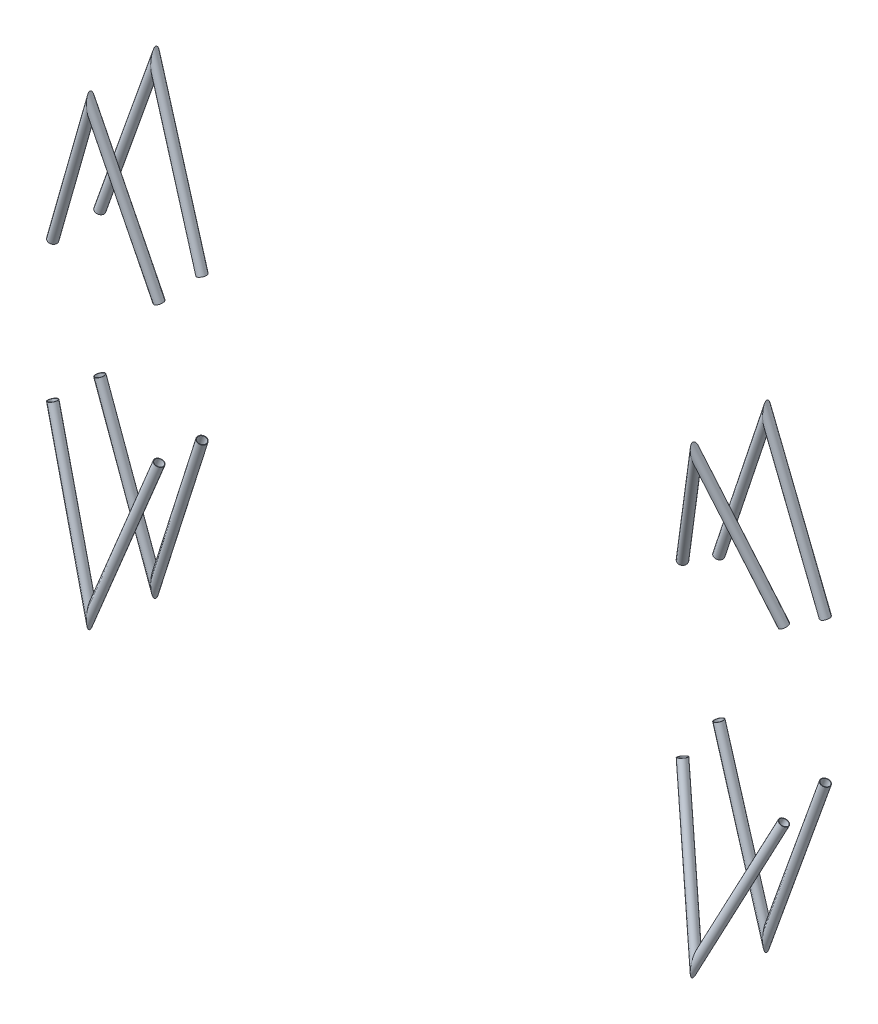
SolidWorks part; units mm, degrees
material "AISI 1015 Steel, Cold Drawn (SS)"
material "AISI 1015 Steel, Cold Drawn (SS)"
material "AISI 1015 Steel, Cold Drawn (SS)"
material "AISI 1015 Steel, Cold Drawn (SS)"
material "AISI 1015 Steel, Cold Drawn (SS)"
material "AISI 1015 Steel, Cold Drawn (SS)"
material "AISI 1015 Steel, Cold Drawn (SS)"
material "AISI 1015 Steel, Cold Drawn (SS)"
material "AISI 1015 Steel, Cold Drawn (SS)"
ref_plane "Ground Plane" through (0, 0, 0) normal (0, 0, 1) x (1, 0, 0)
ref_plane "Side Plane" through (0, 0, 0) normal (0, 1, 0) x (1, 0, 0)
ref_plane "Rear Axel Centerline" through (0, 0, 0) normal (1, 0, 0) x (0, 0, -1)
ref_plane "Front Axel Centerline" through (1700, 0, 0) normal (1, 0, 0) x (0, 0, -1)
sketch "Chassis Side View" plane through (0, 0, 0) normal (0, 1, 0) x (1, 0, 0)
  line L0 (0, -100.53) -> (1700, -100.53) construction
  line L1 (850, -100.53) -> (850, -280)
  line L2 (0, -127.1843) -> (0, 127.1843) construction
  line L3 (-786.3928, 0) -> (786.3928, 0) construction
  line L4 (1550, -100.53) -> (1550, -346.3589) construction
  line L5 (1550, -100.53) -> (1550, -595.53) construction
  line L6 (650, -100.53) -> (650, -1216.53) construction
  line L7 (150, -100.53) -> (150, -312.2598) construction
  line L8 (-150, -100.53) -> (-150, -312.2598) construction
  line L9 (1850, -100.53) -> (1850, -346.3589) construction
  line L10 (0, -100.53) -> (150, -100.53) construction
  line L11 (1700, -100.53) -> (2450, -100.53) construction
  line L12 (2450, -100.53) -> (2450, -450.53) construction
  line L13 (2450, -450.53) -> (1550, -545.53) construction
  line L14 (150, -100.53) -> (150, -400.53) construction
  dimension "D1" = 1700
  dimension "D3" = 850
  dimension "D4" = 100.53
  dimension "D5" = 150
  dimension "D6" = 150
  dimension "D7" = 150
  dimension "D8" = 150
  dimension "D2" = 280
  dimension "D9" = 900
  dimension "D10" = 1116
  dimension "D11" = 495
  dimension "D12" = 350
  dimension "D13" = 900
  dimension "D14" = 50
  dimension "D15" = 300
  dimension "D16" = 500
sketch "Front Wheel Assy Constraints" plane through (1700, 0, 0) normal (1, 0, 0) x (0, 0, -1)
  line L0 (1.6623, 571.529) -> (-1.6623, 762)
  line L2 (-1.6623, 762) -> (-222.6087, 758.1434)
  line L3 (-451.1739, 754.1537) -> (-447.8492, 563.6828)
  line L4 (-222.6087, 758.1434) -> (-451.1739, 754.1537)
  line L5 (-447.8492, 563.6828) -> (-333.5666, 565.6776)
  line L10 (-105.0014, 569.6672) -> (1.6623, 571.529)
  line L11 (-449.5115, 658.9183) -> (0, 666.7645) construction
  line L12 (-222.6087, 758.1434) -> (-221.0572, 669.2569) construction
  line L13 (-107.0128, 684.8996) -> (-335.578, 680.91)
  line L14 (-335.578, 680.91) -> (-333.5666, 565.6776)
  line L15 (-107.0128, 684.8996) -> (-105.0014, 569.6672)
  line L16 (0, 786.3928) -> (0, -786.3928) construction
  line L17 (0, 0) -> (-792.1695, 0) construction
  point P12 (-221.2954, 682.9048)
  dimension "D1" = 190.5
  dimension "D2" = 228.6
  dimension "D3" = 220.98
  dimension "D4" = 228.6
  dimension "D5" = 20
  dimension "D6" = 1
  dimension "D7" = 1524
sketch "Rear Wheel Assy Constaints" plane through (0, 0, 0) normal (1, 0, 0) x (0, 0, -1)
  line L0 (-447.8492, 563.6828) -> (-451.1739, 754.1537)
  line L1 (-451.1739, 754.1537) -> (-222.6087, 758.1434)
  line L2 (-1.6623, 762) -> (1.6623, 571.529)
  line L3 (1.6623, 571.529) -> (-105.0014, 569.6672)
  line L4 (-105.0014, 569.6672) -> (-107.0128, 684.8996)
  line L5 (-107.0128, 684.8996) -> (-335.578, 680.91)
  line L6 (-335.578, 680.91) -> (-333.5666, 565.6776)
  line L7 (-333.5666, 565.6776) -> (-447.8492, 563.6828)
  line L8 (-449.5115, 658.9183) -> (0, 666.7645) construction
  line L9 (0, 0) -> (-789.3704, 0) construction
  line L10 (-221.0572, 669.2569) -> (-222.6087, 758.1434) construction
  line L11 (0, 786.3928) -> (0, -786.3928) construction
  line L12 (-0.0435, 669.2569) -> (-772.6175, 669.2569) construction
  line L13 (-222.6087, 758.1434) -> (-1.6623, 762)
  point P18 (-106.0071, 627.2834)
  point P19 (-221.2954, 682.9048)
  dimension "D1" = 228.6
  dimension "D2" = 220.98
  dimension "D3" = 20
  dimension "D4" = 1524
  dimension "D5" = 1
  dimension "D6" = 228.6
  dimension "D7" = 190.5
sketch "Front Sus Front View" plane through (1700, 0, 0) normal (1, 0, 0) x (0, 0, -1)
  line L0 (0, 666.7645) -> (0, 641.3645) construction
  line L1 (0, 641.3645) -> (-437.8219, 641.3645) construction
  line L2 (0, 641.3645) -> (-427.6307, 603.9517) construction
  line L3 (-305.1173, 614.6702) -> (-210.3608, 238.5)
  line L4 (-73.9022, -303.2224) -> (0, 666.7645) construction
  line L5 (-73.9022, -303.2224) -> (-101.6418, 200.0264) construction
  line L6 (-210.3608, 238.5) -> (-73.9022, -303.2224) construction
  line L7 (-101.6418, 200.0264) -> (-125.3644, 630.3965)
  line L8 (0, 0) -> (-50.8, 0) construction
  line L12 (-222.6087, 758.1434) -> (-221.0572, 669.2569) construction
  dimension "D1" = 25.4
  dimension "D2" = 5
  dimension "D4" = 969.9869
  dimension "D5" = 95
  dimension "D6" = 85
  dimension "D7" = 477
  dimension "D8" = 387.9211
  dimension "D9" = 431.0235
  dimension "D3" = 50.8
sketch "Rear Sus Front View" plane through (0, 0, 0) normal (1, 0, 0) x (0, 0, -1)
  line L0 (0, 666.7645) -> (0, 641.3645) construction
  line L1 (0, 641.3645) -> (-652.2854, 641.3645) construction
  line L2 (0, 641.3645) -> (-647.6734, 584.7004) construction
  line L3 (-305.1173, 614.6702) -> (-263.5724, 194.7562)
  line L4 (-166.3015, -788.4055) -> (-137.7828, 200) construction
  line L5 (-166.3015, -788.4055) -> (0, 666.7645) construction
  line L6 (-263.5724, 194.7562) -> (-166.3015, -788.4055) construction
  line L7 (-137.7828, 200) -> (-125.3644, 630.3965)
  line L8 (0, 0) -> (-76.2, 0) construction
  line L9 (-221.0572, 669.2569) -> (-222.6087, 758.1434) construction
  dimension "D1" = 25.4
  dimension "D2" = 5
  dimension "D5" = 95
  dimension "D6" = 85
  dimension "D3" = 76.2
  dimension "D4" = 1455.17
  dimension "D7" = 400
  dimension "D8" = 430.5757
  dimension "D9" = 421.9641
ref_plane "Front Wheel Side View Plane" through (0, 669.2569, 0) normal (0, 1, 0) x (1, 0, 0)
sketch "Front SVSA" plane through (0, 669.2569, 0) normal (0, 1, 0) x (1, 0, 0)
  line L0 (1731.3585, 77.2994) -> (1668.6415, -519.4137)
  line L1 (1700, -0.0435) -> (-2300, -97.8014) construction
  line L2 (1700, -0.0435) -> (1700, -815.7612) construction
  line L3 (-2300, -97.8014) -> (1700, -221.0572) construction
  line L6 (-786.3928, 0) -> (786.3928, 0) construction
  point P5 (1700, -221.0572)
  dimension "D1" = 600
  dimension "D2" = 6
  dimension "D3" = 1.4
  dimension "D4" = 4000
ref_plane "Rear Wheel Side View Plane" through (0, 669.2569, 0) normal (0, 1, 0) x (1, 0, 0)
sketch "Rear SVSA" plane through (0, 669.2569, 0) normal (0, 1, 0) x (1, 0, 0)
  line L0 (0, -0.0435) -> (0, -772.6175) construction
  line L3 (0, -221.0572) -> (4820.2153, -353.1722) construction
  line L4 (4820.2153, -353.1722) -> (0, -0.0435) construction
  line L5 (-786.3928, 0) -> (786.3928, 0) construction
  line L6 (0, -127.1843) -> (0, 127.1843) construction
  dimension "D1" = 4.19
  dimension "D2" = 1.57
  dimension "D3" = 4820.2153
sketch3d "Front Chassis Side Axis"
  line L0 (1700, 200.0264, 101.6418) -> (1700, 630.3965, 125.3644) construction
  line L1 (1700, 614.6702, 305.1173) -> (1700, 238.5, 210.3608) construction
  line L2 (1700, 200.0264, 101.6418) -> (1700, 630.3965, 125.3644) construction
  line L3 (1700, 614.6702, 305.1173) -> (1700, 238.5, 210.3608) construction
  line L4 (1700, 614.6702, 305.1173) -> (1700, 669.2569, 318.8676) construction
  line L5 (1700, 630.3965, 125.3644) -> (1700, 669.2569, 127.5064) construction
  line L6 (-2300, 669.2569, 97.8014) -> (1749.9238, 669.2569, 321.6267) construction
  line L7 (-2300, 669.2569, 97.8014) -> (1749.9986, 669.2569, 127.8777) construction
  line L8 (1749.9238, 669.2569, 321.6267) -> (1355.9629, 238.5, 191.3471) construction
  line L9 (1749.9986, 669.2569, 127.8777) -> (1146.276, 200.0264, 97.5298) construction
  line L10 (1700, 238.5, 210.3608) -> (1700, 238.5, 191.3471) construction
  line L11 (1700, 238.5, 191.3471) -> (1355.9629, 238.5, 191.3471) construction
  line L12 (1999.5429, 238.5, 226.9155) -> (1056.42, 238.5, 174.7924)
  line L13 (1700, 200.0264, 101.6418) -> (1700, 200.0264, 97.5298) construction
  line L14 (1700, 200.0264, 97.5298) -> (582.2888, 200.0264, 97.5298) construction
  line L15 (1999.9917, 200.0264, 103.8697) -> (846.2843, 200.0264, 95.3019)
  dimension "D1" = 50
  dimension "D2" = 50
  dimension "D3" = 300
  dimension "D4" = 300
  dimension "D5" = 300
  dimension "D6" = 300
sketch3d "Rear Chassis Side Axis"
  line L0 (0, 200, 137.7828) -> (0, 630.3965, 125.3644) construction
  line L1 (0, 614.6702, 305.1173) -> (0, 194.7562, 263.5724) construction
  line L2 (0, 200, 137.7828) -> (0, 630.3965, 125.3644) construction
  line L3 (0, 614.6702, 305.1173) -> (0, 194.7562, 263.5724) construction
  line L4 (0, 614.6702, 305.1173) -> (0, 669.2569, 310.5179) construction
  line L5 (0, 630.3965, 125.3644) -> (0, 669.2569, 124.2431) construction
  line L6 (4820.2153, 669.2569, 353.1722) -> (-24.999, 669.2569, 310.2967) construction
  line L7 (4820.2153, 669.2569, 353.1722) -> (-19.9775, 669.2569, 123.2943) construction
  line L8 (-24.999, 669.2569, 310.2967) -> (192.3076, 194.7562, 265.2741) construction
  line L9 (-19.9775, 669.2569, 123.2943) -> (221.2599, 200, 148.2912) construction
  line L10 (0, 194.7562, 263.5724) -> (0, 194.7562, 265.2741) construction
  line L11 (0, 194.7562, 265.2741) -> (192.3076, 194.7562, 265.2741) construction
  line L12 (0, 200, 137.7828) -> (0, 200, 148.2912) construction
  line L13 (0, 200, 148.2912) -> (221.2599, 200, 148.2912) construction
  line L14 (492.2959, 194.7562, 267.9287) -> (-299.9883, 194.7562, 260.9178)
  line L15 (520.9221, 200, 162.5232) -> (-299.6622, 200, 123.5507)
  dimension "D1" = 25
  dimension "D2" = 20
  dimension "D3" = 300
  dimension "D4" = 300
  dimension "D5" = 300
  dimension "D6" = 300
sketch3d "Front Control Arm"
  line L1 (1700, 614.6702, 305.1173) -> (1700, 238.5, 210.3608) construction
  line L2 (1700, 200.0264, 101.6418) -> (1700, 630.3965, 125.3644) construction
  line L3 (1700, 614.6702, 305.1173) -> (1700, 238.5, 210.3608) construction
  line L4 (1999.9917, 200.0264, 103.8697) -> (846.2843, 200.0264, 95.3019) construction
  line L5 (1999.5429, 238.5, 226.9155) -> (1056.42, 238.5, 174.7924) construction
  line L6 (1999.9917, 200.0264, 103.8697) -> (846.2843, 200.0264, 95.3019) construction
  line L7 (1999.5429, 238.5, 226.9155) -> (1056.42, 238.5, 174.7924) construction
  line L8 (1850, 238.5, 218.6508) -> (1689.7791, 614.6702, 304.5524)
  line L9 (1689.7791, 614.6702, 304.5524) -> (1550, 238.5, 202.0709)
  line L10 (1700, 614.6702, 305.1173) -> (1689.7791, 614.6702, 304.5524) construction
  line L11 (1689.7791, 669.2569, 318.3027) -> (1689.7791, 614.6702, 304.5524) construction
  line L12 (1731.3585, 669.2569, -77.2994) -> (1668.6415, 669.2569, 519.4137) construction
  line L13 (1850, 0, 218.6508) -> (1850, 238.5, 218.6508) construction
  line L14 (1850, 0, 100.53) -> (1850, 0, 346.3589) construction
  line L15 (1550, 0, 202.0709) -> (1550, 238.5, 202.0709) construction
  line L16 (1550, 0, 100.53) -> (1550, 0, 346.3589) construction
  line L17 (1850, 200.0264, 102.7558) -> (1709.8249, 630.3965, 125.4373)
  line L18 (1709.8249, 630.3965, 125.4373) -> (1550, 200.0264, 100.5279)
  line L19 (1850, 0, 102.7558) -> (1850, 200.0264, 102.7558) construction
  line L20 (1550, 0, 100.5279) -> (1550, 200.0264, 100.5279) construction
  line L21 (1709.8249, 630.3965, 125.4373) -> (1709.8249, 669.2569, 127.5794) construction
  line L22 (1709.8249, 630.3965, 125.4373) -> (1700, 630.3965, 125.3644) construction
  line L23 (1700, 200.0264, 101.6418) -> (1700, 630.3965, 125.3644) construction
sketch3d "Rear Control Arm"
  line L0 (0, 614.6702, 305.1173) -> (0, 194.7562, 263.5724) construction
  line L1 (0, 200, 137.7828) -> (0, 630.3965, 125.3644) construction
  line L2 (0, 614.6702, 305.1173) -> (0, 194.7562, 263.5724) construction
  line L3 (0, 200, 137.7828) -> (0, 630.3965, 125.3644) construction
  line L4 (492.2959, 194.7562, 267.9287) -> (-299.9883, 194.7562, 260.9178) construction
  line L5 (520.9221, 200, 162.5232) -> (-299.6622, 200, 123.5507) construction
  line L6 (492.2959, 194.7562, 267.9287) -> (-299.9883, 194.7562, 260.9178) construction
  line L7 (520.9221, 200, 162.5232) -> (-299.6622, 200, 123.5507) construction
  line L8 (150, 194.7562, 264.8997) -> (0, 614.6702, 305.1173)
  line L9 (0, 614.6702, 305.1173) -> (-150, 194.7562, 262.245)
  line L10 (150, 200, 144.9068) -> (0, 630.3965, 125.3644)
  line L11 (0, 630.3965, 125.3644) -> (-150, 200, 130.6587)
  line L12 (-150, 0, 262.245) -> (-150, 194.7562, 262.245) construction
  line L13 (-150, 0, 100.53) -> (-150, 0, 312.2598) construction
  line L14 (-150, 0, 130.6587) -> (-150, 200, 130.6587) construction
  line L15 (150, 0, 264.8997) -> (150, 194.7562, 264.8997) construction
  line L16 (150, 0, 100.53) -> (150, 0, 312.2598) construction
  line L17 (150, 0, 144.9068) -> (150, 200, 144.9068) construction
sketch3d "3DSketch1"
  line L0 (1689.7791, 614.6702, 304.5524) -> (1854.9137, 226.9636, 216.0164) construction
  dimension "D1" = 12.813
sketch3d "Control Arms"
  line L0 (0, 614.6702, 305.1173) -> (-150, 194.7562, 262.245) construction
  line L1 (150, 200, 144.9068) -> (0, 630.3965, 125.3644) construction
  line L2 (0, 630.3965, 125.3644) -> (-150, 200, 130.6587) construction
  line L3 (150, 194.7562, 264.8997) -> (0, 614.6702, 305.1173) construction
  line L4 (1850, 238.5, 218.6508) -> (1689.7791, 614.6702, 304.5524) construction
  line L5 (1689.7791, 614.6702, 304.5524) -> (1550, 238.5, 202.0709) construction
  line L6 (1709.8249, 630.3965, 125.4373) -> (1550, 200.0264, 100.5279) construction
  line L7 (1850, 200.0264, 102.7558) -> (1709.8249, 630.3965, 125.4373) construction
  line L8 (0, 614.6702, 305.1173) -> (-150, 194.7562, 262.245)
  line L9 (1850, 200.0264, 102.7558) -> (1709.8249, 630.3965, 125.4373)
  line L10 (1689.7791, 614.6702, 304.5524) -> (1550, 238.5, 202.0709)
  line L11 (1709.8249, 630.3965, 125.4373) -> (1550, 200.0264, 100.5279)
  line L12 (1850, 238.5, 218.6508) -> (1689.7791, 614.6702, 304.5524)
  line L13 (150, 194.7562, 264.8997) -> (0, 614.6702, 305.1173)
  line L14 (0, 630.3965, 125.3644) -> (-150, 200, 130.6587)
  line L15 (150, 200, 144.9068) -> (0, 630.3965, 125.3644)
  line L16 (0, -614.6702, 305.1173) -> (-150, -194.7562, 262.245)
  line L17 (150, -194.7562, 264.8997) -> (0, -614.6702, 305.1173)
  line L18 (0, -630.3965, 125.3644) -> (-150, -200, 130.6587)
  line L19 (150, -200, 144.9068) -> (0, -630.3965, 125.3644)
  line L20 (1850, -200.0264, 102.7558) -> (1709.8249, -630.3965, 125.4373)
  line L21 (1709.8249, -630.3965, 125.4373) -> (1550, -200.0264, 100.5279)
  line L22 (1850, -238.5, 218.6508) -> (1689.7791, -614.6702, 304.5524)
  line L23 (1689.7791, -614.6702, 304.5524) -> (1550, -238.5, 202.0709)
sketch "Sketch2" plane through (0, 0, 0) normal (1, 0, 0) x (0, 0, -1)
  line L0 (-505.8721, 230.5581) -> (-420, 175)
  line L1 (-420, 175) -> (-420, -175) construction
  line L2 (0, 0) -> (-792.1695, 0) construction
  line L3 (-420, 0) -> (0, 0) construction
  line L4 (-505.8721, -230.5581) -> (-420, -175)
  line L5 (0, 786.3928) -> (0, -786.3928) construction
  line L6 (-420, 175) -> (-125.3644, 630.3965) construction
  dimension "D1" = 350
  dimension "D2" = 420
  dimension "D3" = 57.098
ref_plane "Rear Bell Crank Pivot" through (0, 175, 420) normal (0, 0.5432, 0.8396) x (1, 0, 0)
ref_plane "Plane2" through (1575, 0, 0) normal (1, 0, 0) x (0, 0, -1)
sketch3d "Control Arms - Droop"
  line L0 (150, 200, 144.9068) -> (1.3061, 628.7192, 97.8632)
  line L1 (1.3061, 628.7192, 97.8632) -> (-150, 200, 130.6587)
  line L2 (150, 194.7562, 264.8997) -> (0.241, 616.4775, 277.8839)
  line L3 (0.241, 616.4775, 277.8839) -> (-150, 194.7562, 262.245)
  line L4 (150, 194.7562, 264.8997) -> (0, 614.6702, 305.1173) construction
  line L5 (0, 614.6702, 305.1173) -> (-150, 194.7562, 262.245) construction
  line L6 (150, 200, 144.9068) -> (0, 630.3965, 125.3644) construction
  line L7 (0, 630.3965, 125.3644) -> (-150, 200, 130.6587) construction
  line L8 (0, 630.3965, 125.3644) -> (0, 614.6702, 305.1173) construction
  line L9 (0, 614.6702, 305.1173) -> (0, 758.1434, 222.6087) construction
  line L10 (0, 758.1434, 222.6087) -> (0, 630.3965, 125.3644) construction
  line L11 (1.3061, 628.7192, 97.8632) -> (0.241, 616.4775, 277.8839) construction
  line L12 (0.241, 616.4775, 277.8839) -> (0, 758.3236, 192.6087) construction
  line L13 (0, 758.3236, 192.6087) -> (1.3061, 628.7192, 97.8632) construction
  line L15 (1850, 200.0264, 102.7558) -> (1710.0211, 631.0414, 99.0206)
  line L16 (1710.0211, 631.0414, 99.0206) -> (1550, 200.0264, 100.5279)
  line L17 (1850, 238.5, 218.6508) -> (1691.2114, 620.2616, 278.635)
  line L18 (1691.2114, 620.2616, 278.635) -> (1550, 238.5, 202.0709)
  line L19 (1689.7791, 614.6702, 304.5524) -> (1550, 238.5, 202.0709) construction
  line L20 (1850, 238.5, 218.6508) -> (1689.7791, 614.6702, 304.5524) construction
  line L21 (1709.8249, 630.3965, 125.4373) -> (1550, 200.0264, 100.5279) construction
  line L22 (1850, 200.0264, 102.7558) -> (1709.8249, 630.3965, 125.4373) construction
  line L23 (1709.8249, 630.3965, 125.4373) -> (1689.7791, 614.6702, 304.5524) construction
  line L24 (1689.7791, 614.6702, 304.5524) -> (1700, 758.1434, 222.6087) construction
  line L25 (1700, 758.1434, 222.6087) -> (1709.8249, 630.3965, 125.4373) construction
  line L26 (1691.2114, 620.2616, 278.635) -> (1710.0211, 631.0414, 99.0206) construction
  line L27 (1710.0211, 631.0414, 99.0206) -> (1700, 761.4212, 192.6087) construction
  line L28 (1700, 761.4212, 192.6087) -> (1691.2114, 620.2616, 278.635) construction
  dimension "D1" = 30
  dimension "D2" = 30
other "Size c tubing FSAE SIZE C TUBING(1)"
ref_plane "Plane3" through (1850, 200.0264, 102.7558) normal (-0.3093, 0.9496, 0.05) x (0.9089, 0.2797, 0.3093)
sketch "Sketch1" plane through (1850, 200.0264, 102.7558) normal (-0.3093, 0.9496, 0.05) x (0.9089, 0.2797, 0.3093)
  circle A0 centre (0, 0) radius 12.5
  circle A1 centre (0, 0) radius 11.3
  point P4 (0, 0)
  dimension "D1" = 25
  dimension "D2" = 1.2
equation "\"Wheelbase\"= 1700mm'Min Req + 1 inch"
equation "\"track_front_outer\"= 60in"
equation "\"track_rear_outer\"= 60in"
equation "\"cg_height\"= 280mm'Placeholder"
equation "\"cg_b\"= \"Wheelbase\" / 2'Placeholder (meas from rear wheel center)"
equation "\"Chassis_ride_height\"= 75'Placeholder"
equation "\"hub_offset_front\"= 20mm'Placeholder"
equation "\"hub_offset_rear\"= 20mm'Placeholder"
equation "\"tire_radius_front\"= 9in'HOOSIER"
equation "\"tire_radius_loaded_front\"= 8.7in'HOOSIER etc"
equation "\"tire_radius_loaded_rear\"= 8.7in"
equation "\"tire_radius_rear\"= 9in"
equation "\"tire_width_front\"= 7.5in"
equation "\"tire_width_rear\"= 7.5in"
equation "\"static_camber_front\"= 1deg"
equation "\"static_camber_rear\"= 1deg'per inch of travel"
equation "\"kingpin_front_static\"= 5deg"
equation "\"caster_front_static\"= 6deg"
equation "\"control_arm_ratio_front\"= .9'L upper / L lower"
equation "\"control_arm_ratio_rear\"= .98'L upper / L lower"
equation "\"roll_center_height_front\"= 2in"
equation "\"roll_center_height_rear\"= 3in"
equation "\"scrub_radius_front\"= 1in"
equation "\"camber_change_rate_front\"= 1.5deg'per inch of travel"
equation "\"camber_change_rate_rear\"= 1deg'per inch of travel"
equation "\"D1@Chassis Side View\" = \"Wheelbase\""
equation "\"D3@Chassis Side View\" = \"cg_b\""
equation "\"D2@Chassis Side View\" = \"cg_height\""
equation "\"D1@Front Axel Centerline\"=\"Wheelbase\""
equation "\"D1@Front Wheel Assy Constraints\" = \"tire_width_front\""
equation "\"D2@Front Wheel Assy Constraints\" = \"tire_radius_front\""
equation "\"D3@Front Wheel Assy Constraints\" = \"tire_radius_loaded_front\""
equation "\"wheel_internal_diameter_front\"= 9in"
equation "\"D4@Front Wheel Assy Constraints\" = \"wheel_internal_diameter_front\""
equation "\"D5@Front Wheel Assy Constraints\" = \"hub_offset_front\""
equation "\"D6@Front Wheel Assy Constraints\" = \"static_camber_front\""
equation "\"D7@Front Wheel Assy Constraints\" = \"track_front_outer\""
equation "\"D1@Rear Wheel Assy Constaints\" = \"tire_radius_rear\""
equation "\"D2@Rear Wheel Assy Constaints\" = \"tire_radius_loaded_rear\""
equation "\"D3@Rear Wheel Assy Constaints\" = \"hub_offset_rear\""
equation "\"D4@Rear Wheel Assy Constaints\" = \"track_rear_outer\""
equation "\"D5@Rear Wheel Assy Constaints\" = \"static_camber_rear\""
equation "\"wheel_internal_diameter_rear\"= 9in"
equation "\"D6@Rear Wheel Assy Constaints\" = \"wheel_internal_diameter_rear\""
equation "\"D7@Rear Wheel Assy Constaints\" = \"tire_width_rear\""
equation "\"D1@Front Sus Front View\" = \"scrub_radius_front\""
equation "\"D2@Front Sus Front View\" = \"kingpin_front_static\""
equation "\"fvsa_length_front\"= 1 / tan ( \"camber_change_rate_front\" ) * 1in"
equation "\"fvsa_length_rear\"= 1 / tan ( \"camber_change_rate_rear\" ) * 1in"
equation "\"D4@Front Sus Front View\" = \"fvsa_length_front\""
equation "\"D9@Front Sus Front View\" = \"D8@Front Sus Front View\" / \"control_arm_ratio_front\""
equation "\"D1@Rear Sus Front View\" = \"scrub_radius_front\""
equation "\"D2@Rear Sus Front View\" = \"kingpin_front_static\""
equation "\"D3@Front Sus Front View\"=\"roll_center_height_front\""
equation "\"D3@Rear Sus Front View\" = \"roll_center_height_rear\""
equation "\"D9@Rear Sus Front View\" = \"D8@Rear Sus Front View\" * \"control_arm_ratio_rear\""
equation "\"anti_squat_rear\"= 0.2'percentage"
equation "\"anti_lift_rear\"= 0.15'percentage"
equation "\"anti_dive_front\"= 0.15'percentage"
equation "\"front_braking\"= 0.75'percentage"
equation "\"rear_braking\"= 1 - ( \"front_braking\" )'percentage"
equation "\"phi_front\"= atn ( \"anti_dive_front\" / \"front_braking\" * \"cg_height\" / \"Wheelbase\" )'angl of ground & linebetween instant center and ground contact"
equation "\"phi_rear\"= atn ( \"anti_lift_rear\" / \"rear_braking\" * \"cg_height\" / \"Wheelbase\" )'angl of ground & linebetween instant center and ground contact"
equation "\"theta_rear\"= atn ( \"anti_squat_rear\" * \"cg_height\" / \"Wheelbase\" )"
